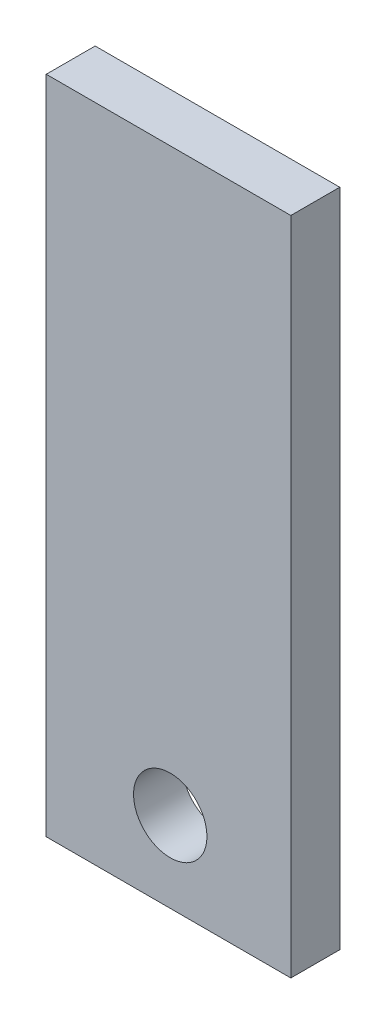
SolidWorks part; units mm, degrees
ref_plane "Alzado" through (0, 0, 0) normal (0, 0, 1) x (1, 0, 0)
ref_plane "Planta" through (0, 0, 0) normal (0, 1, 0) x (1, 0, 0)
ref_plane "Vista lateral" through (0, 0, 0) normal (1, 0, 0) x (0, 0, -1)
sketch "Croquis1" plane through (0, 0, 0) normal (0, 0, 1) x (1, 0, 0)
  line L1 (0, 0) -> (70, 0)
  line L2 (0, 0) -> (0, 189)
  line L3 (0, 189) -> (70, 189)
  line L4 (70, 0) -> (70, 189)
  circle A2 centre (35.49, 23.0406) radius 10.5
  dimension "D3" = 21
  dimension "D1" = 189
  dimension "D2" = 70
  dimension "D4" = 35.49
extrude "Saliente-Extruir3" add sketch "Croquis1" along normal blind 14
ref_plane "Plano1" through (70, 0, 0) normal (0, 1, 0) x (1, 0, 0)
